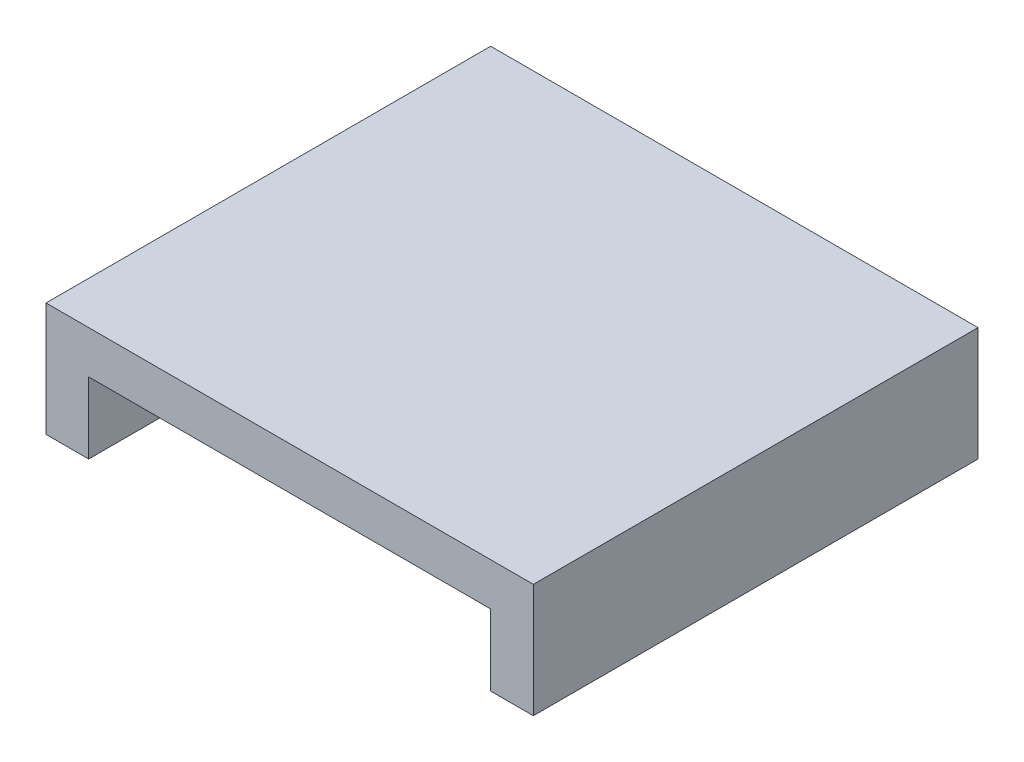
SolidWorks part; units mm, degrees
ref_plane "Front Plane" through (0, 0, 0) normal (0, 0, 1) x (1, 0, 0)
ref_plane "Top Plane" through (0, 0, 0) normal (0, 1, 0) x (1, 0, 0)
ref_plane "Right Plane" through (0, 0, 0) normal (1, 0, 0) x (0, 0, -1)
sketch "Sketch1" plane through (0, 0, 0) normal (0, 1, 0) x (1, 0, 0)
  line L1 (-28.25, -28.25) -> (28.25, -28.25)
  line L2 (-28.25, -28.25) -> (-28.25, 28.25)
  line L3 (-28.25, 28.25) -> (28.25, 28.25)
  line L4 (28.25, -28.25) -> (28.25, 28.25)
  line L5 (-28.25, -28.25) -> (28.25, 28.25) construction
  line L6 (-28.25, 28.25) -> (28.25, -28.25) construction
  point P0 (0, 0)
  dimension "D1" = 56.5
  dimension "D2" = 56.5
extrude "Boss-Extrude1" add sketch "Sketch1" along normal blind 10
shell "Shell1" thickness 6
sketch "Sketch2" plane through (0, 10, 0) normal (0, -1, 0) x (1, 0, 0)
  line L1 (28.25, 28.25) -> (-28.25, 28.25)
  line L2 (28.25, 28.25) -> (28.25, -28.25)
  line L3 (28.25, -28.25) -> (-28.25, -28.25)
  line L4 (-28.25, 28.25) -> (-28.25, -28.25)
  line L5 (28.25, 28.25) -> (-28.25, -28.25) construction
  line L6 (28.25, -28.25) -> (-28.25, 28.25) construction
  point P0 (0, 0)
extrude "Cut-Extrude1" cut sketch "Sketch3" against normal blind 8
sketch "Sketch3" [suppressed] plane through (60.7775, 10, -23.0634) normal (0, -1, 0) x (-1, 0, 0)
  circle A2 centre (69.1775, -31.7134) radius 2.5
  circle A3 centre (52.3775, -31.7134) radius 2.5
